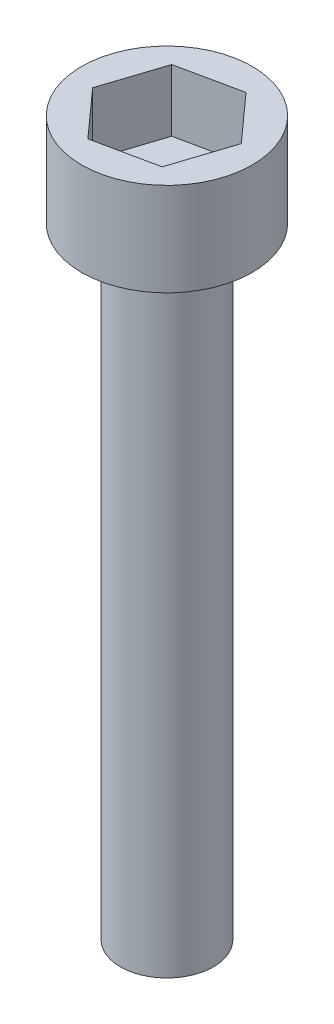
SolidWorks part; units mm, degrees
ref_plane "Front Plane" through (0, 0, 0) normal (0, 0, 1) x (1, 0, 0)
ref_plane "Top Plane" through (0, 0, 0) normal (0, 1, 0) x (1, 0, 0)
ref_plane "Right Plane" through (0, 0, 0) normal (1, 0, 0) x (0, 0, -1)
sketch "Sketch1" plane through (0, 0, 0) normal (0, 1, 0) x (1, 0, 0)
  circle A0 centre (0, 0) radius 1.5
extrude "Boss-Extrude1" add sketch "Sketch1" along normal blind 20
sketch "Sketch2" plane through (0, 20, 0) normal (0, 1, 0) x (1, 0, 0)
  circle A0 centre (0, 0) radius 2.75
extrude "Boss-Extrude2" add sketch "Sketch2" along normal blind 3
sketch "Sketch4" plane through (0, 23, 0) normal (0, 1, 0) x (1, 0, 0)
  line L1 (1.9772, 0.4174) -> (0.6271, 1.9209)
  line L2 (0.6271, 1.9209) -> (-1.35, 1.5036)
  line L3 (-1.35, 1.5036) -> (-1.9772, -0.4174)
  line L4 (-1.9772, -0.4174) -> (-0.6271, -1.9209)
  line L5 (-0.6271, -1.9209) -> (1.35, -1.5036)
  line L6 (1.35, -1.5036) -> (1.9772, 0.4174)
  circle A0 centre (0, 0) radius 1.75 construction
extrude "Cut-Extrude1" cut sketch "Sketch4" against normal blind 2
